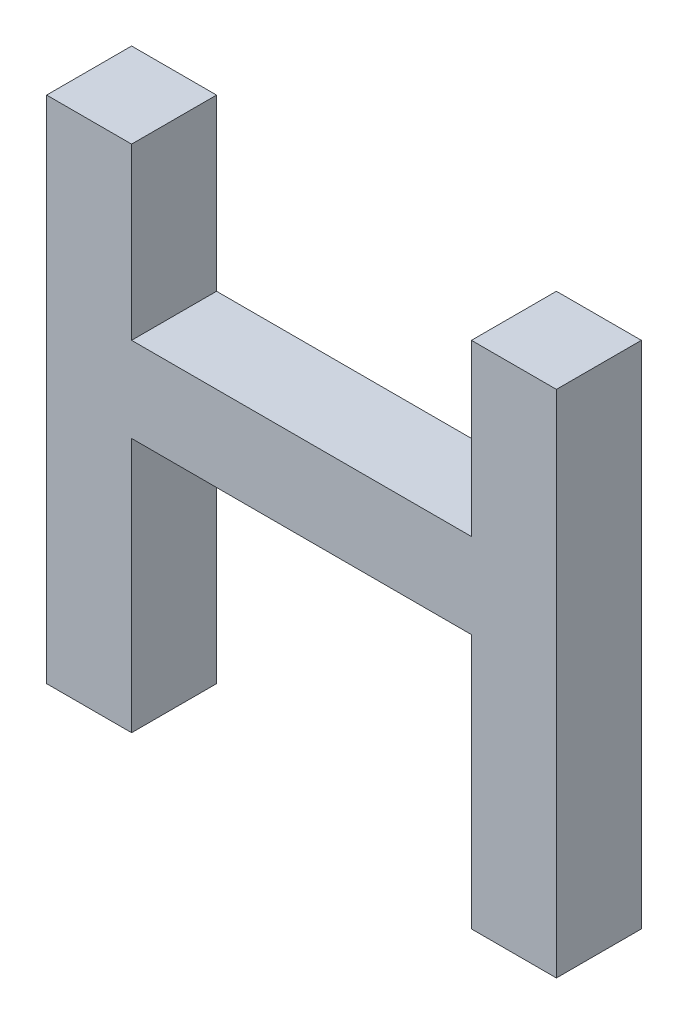
SolidWorks part; units mm, degrees
ref_plane "Front Plane" through (0, 0, 0) normal (0, 0, 1) x (1, 0, 0)
ref_plane "Top Plane" through (0, 0, 0) normal (0, 1, 0) x (1, 0, 0)
ref_plane "Right Plane" through (0, 0, 0) normal (1, 0, 0) x (0, 0, -1)
sketch "Sketch1" plane through (0, 0, 0) normal (0, 0, 1) x (1, 0, 0)
  line L0 (50.8, 0) -> (-50.8, 0)
  line L1 (-50.8, 0) -> (-50.8, -76.2)
  line L2 (-50.8, -76.2) -> (-76.2, -76.2)
  line L3 (-76.2, -76.2) -> (-76.2, 76.2)
  line L4 (-76.2, 76.2) -> (-50.8, 76.2)
  line L5 (-50.8, 76.2) -> (-50.8, 25.4)
  line L6 (-50.8, 25.4) -> (50.8, 25.4)
  line L7 (0, 111.3824) -> (0, -96.9662) construction
  line L8 (50.8, 76.2) -> (50.8, 25.4)
  line L9 (76.2, 76.2) -> (50.8, 76.2)
  line L10 (76.2, -76.2) -> (76.2, 76.2)
  line L11 (50.8, -76.2) -> (76.2, -76.2)
  line L12 (50.8, 0) -> (50.8, -76.2)
  point P14 (0, 25.4)
  point P19 (0, 0)
  dimension "D1" = 25.4
  dimension "D2" = 152.4
  dimension "D3" = 50.8
  dimension "D4" = 50.8
  dimension "D5" = 25.4
extrude "Boss-Extrude1" add sketch "Sketch1" along normal blind 25.4
